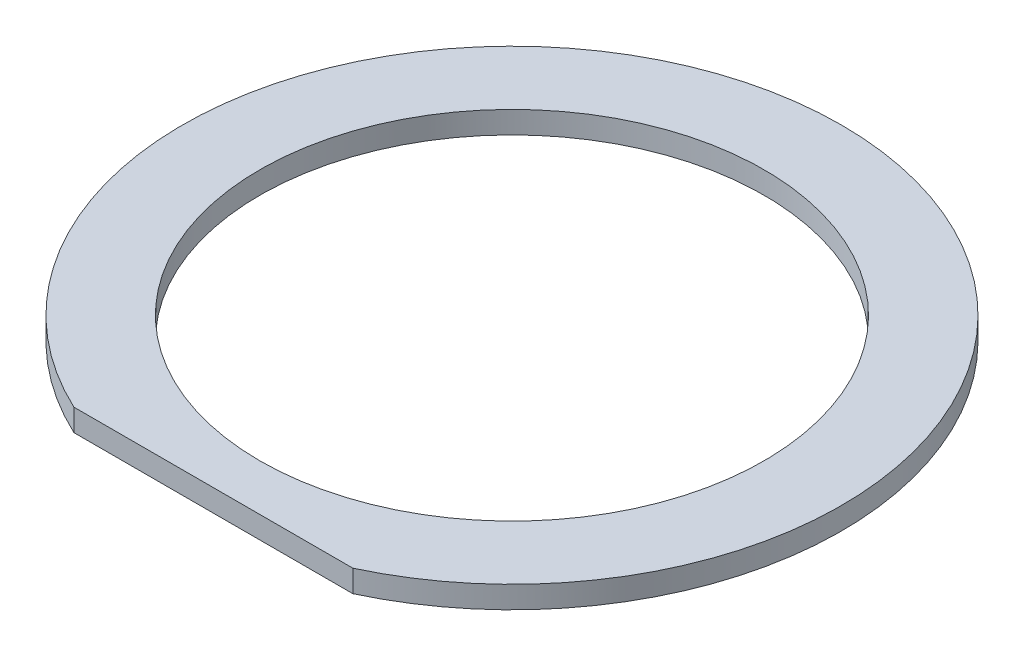
SolidWorks part; units mm, degrees
ref_plane "YZ" through (0, 0, 0) normal (0, 0, 1) x (1, 0, 0)
ref_plane "XY" through (0, 0, 0) normal (0, 1, 0) x (1, 0, 0)
ref_plane "XZ" through (0, 0, 0) normal (1, 0, 0) x (0, 0, -1)
sketch "Sketch1" plane through (0, 0, 0) normal (0, 1, 0) x (1, 0, 0)
  line L0 (-8.0081, -17.145) -> (8.0081, -17.145)
  arc A0 (8.0081, -17.145) -> (-8.0081, -17.145) centre (0, 0) ccw
  circle A1 centre (0, 0) radius 14.478
  dimension "D1" = 37.846
  dimension "D2" = 28.956
  dimension "D3" = 17.145
extrude "Base-Extrude" add sketch "Sketch1" along normal blind 1.27
